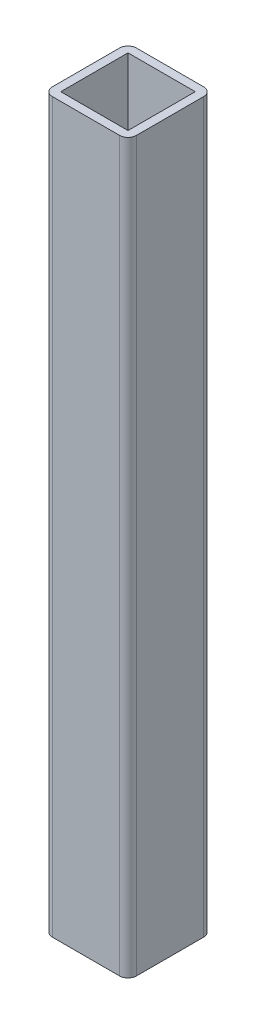
SolidWorks part; units mm, degrees
ref_plane "Alzado" through (0, 0, 0) normal (0, 0, 1) x (1, 0, 0)
ref_plane "Planta" through (0, 0, 0) normal (0, 1, 0) x (1, 0, 0)
ref_plane "Vista lateral" through (0, 0, 0) normal (1, 0, 0) x (0, 0, -1)
ref_plane "Plano1" through (0, 647.65, 0) normal (0, 1, 0) x (1, 0, 0)
sketch "Croquis1" plane through (0, 647.65, 0) normal (0, 1, 0) x (1, 0, 0)
  line L0 (12, 53.1201) -> (-12, 53.1201)
  line L1 (-12, 53.1201) -> (-12, 77.1201)
  line L2 (-12, 77.1201) -> (12, 77.1201)
  line L3 (12, 77.1201) -> (12, 53.1201)
  line L4 (-12, 50.1201) -> (12, 50.1201)
  line L5 (15, 53.1201) -> (15, 77.1201)
  line L6 (12, 80.1201) -> (-12, 80.1201)
  line L7 (-15, 77.1201) -> (-15, 53.1201)
  arc A0 (12, 50.1201) -> (15, 53.1201) centre (12, 53.1201) ccw
  arc A1 (15, 77.1201) -> (12, 80.1201) centre (12, 77.1201) ccw
  arc A2 (-12, 80.1201) -> (-15, 77.1201) centre (-12, 77.1201) ccw
  arc A3 (-15, 53.1201) -> (-12, 50.1201) centre (-12, 53.1201) ccw
extrude "Saliente-Extruir1" add sketch "Croquis1" against normal blind 259.7155
